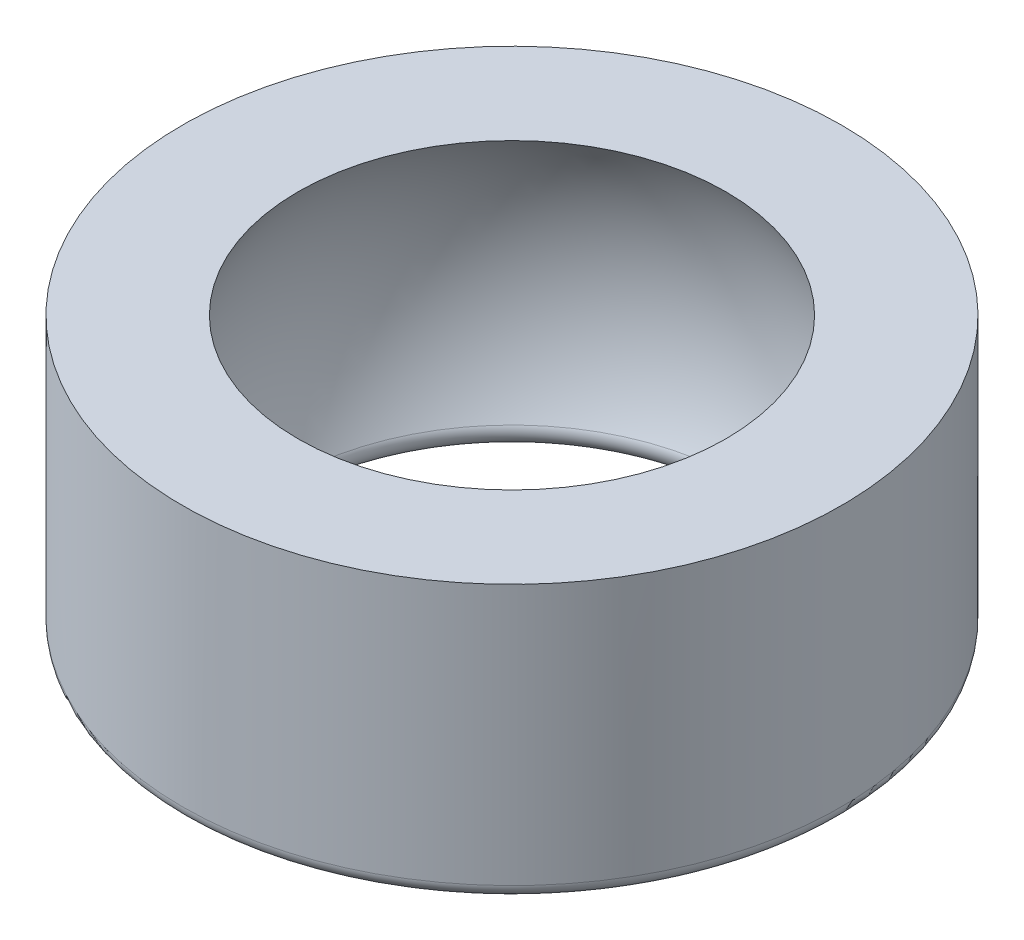
SolidWorks part; units mm, degrees
ref_plane "Front Plane" through (0, 0, 0) normal (0, 0, 1) x (1, 0, 0)
ref_plane "Top Plane" through (0, 0, 0) normal (0, 1, 0) x (1, 0, 0)
ref_plane "Right Plane" through (0, 0, 0) normal (1, 0, 0) x (0, 0, -1)
sketch "Sketch1" plane through (0, 0, 0) normal (0, 0, 1) x (1, 0, 0)
  line L0 (-4.6753, 3) -> (-7.2, 3)
  line L1 (-7.2, 3) -> (-7.2, -3)
  line L2 (-7.2, -3) -> (-4.6753, -3)
  line L3 (0, -3.8098) -> (0, 4.3081) construction
  line L4 (0, 0) -> (-7.2, 3) construction
  arc A0 (-4.6753, 3) -> (-4.6753, -3) centre (0, 0) ccw
  point P5 (-7.2, 0)
  dimension "D1" = 11.11
  dimension "D2" = 6
  dimension "D3" = 7.8
revolve "Revolve1" add sketch "Sketch1" angle 360 about L3
fillet "Fillet1" radius 0.3 1 edges at (0, -3, -4.6753)
fillet "Fillet2" radius 0.3 1 edges at (0, -3, -7.2)
